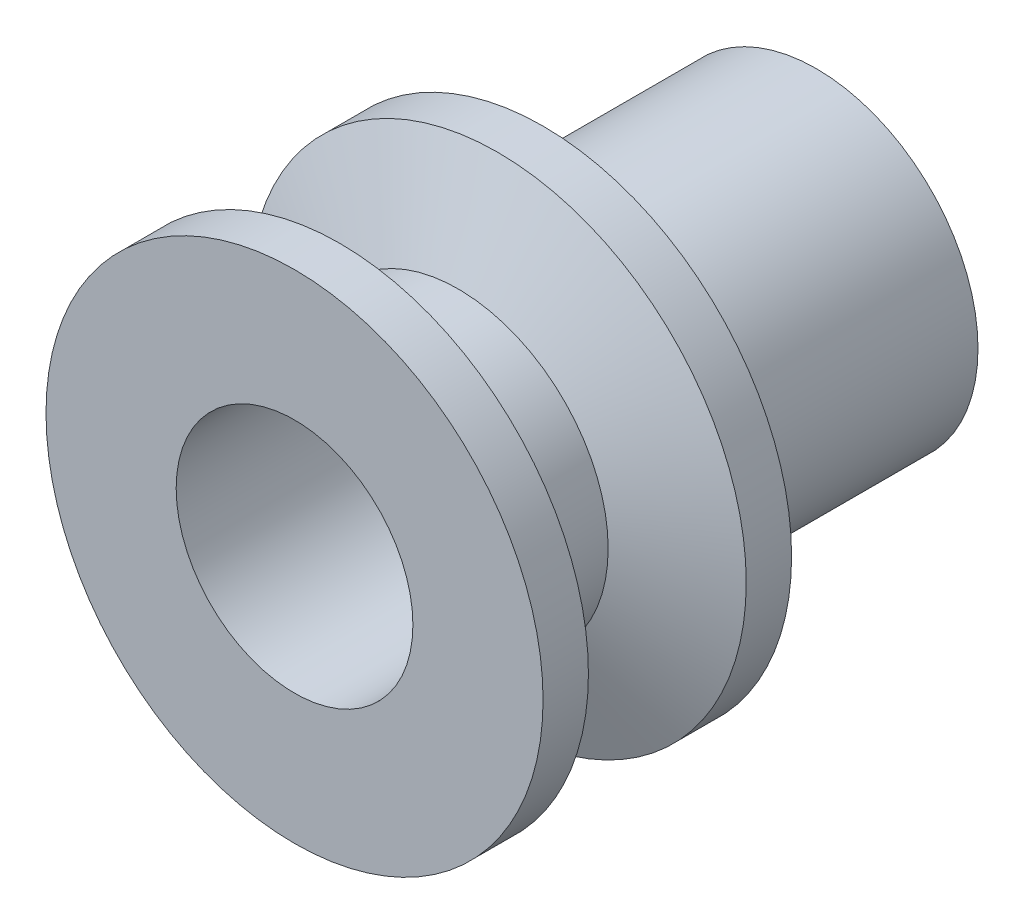
SolidWorks part; units mm, degrees
ref_plane "Alzado" through (0, 0, 0) normal (0, 0, 1) x (1, 0, 0)
ref_plane "Planta" through (0, 0, 0) normal (0, 1, 0) x (1, 0, 0)
ref_plane "Vista lateral" through (0, 0, 0) normal (1, 0, 0) x (0, 0, -1)
sketch "Croquis2" plane through (0, 0, 0) normal (0, 1, 0) x (1, 0, 0)
  line L0 (0, 0) -> (0, 42) construction
  line L1 (20, 0) -> (20, 3.65)
  line L2 (20, 3.65) -> (12.0625, 6.825)
  line L3 (12.0625, 6.825) -> (12.0625, 13.175)
  line L4 (12.0625, 13.175) -> (20, 16.35)
  line L5 (20, 16.35) -> (20, 20)
  line L6 (20, 20) -> (13, 20)
  line L7 (13, 20) -> (13, 42)
  line L8 (13, 42) -> (9.525, 42)
  line L9 (9.525, 42) -> (9.525, 0)
  line L10 (9.525, 0) -> (20, 0)
  point P5 (21.4262, 6.4722)
  point P14 (21.9367, 8.0099)
  point P15 (7.9375, 44.7571)
  point P16 (0, 0)
  point P17 (11.0625, 17.0595)
  point P18 (11.0625, 12.696)
  dimension "D1" = 9.525
  dimension "D2" = 20
  dimension "D3" = 42
  dimension "D4" = 12.7
  dimension "D5" = 7.9375
  dimension "D6" = 13
  dimension "D7" = 20
  dimension "D8" = 6.35
revolve "Revolución2" add sketch "Croquis2" angle 360 about L0
sketch "Croquis7" plane through (0, 0, 0) normal (0, 1, 0) x (1, 0, 0)
  line L0 (13, 42) -> (-13, 42) construction
  circle A0 centre (0, 32) radius 3.175
  point P2 (-1.9045, 31.6018)
  dimension "D2" = 6.35
  dimension "D1" = 10
extrude "Cortar-Extruir2" cut sketch "Croquis7" against normal through all
